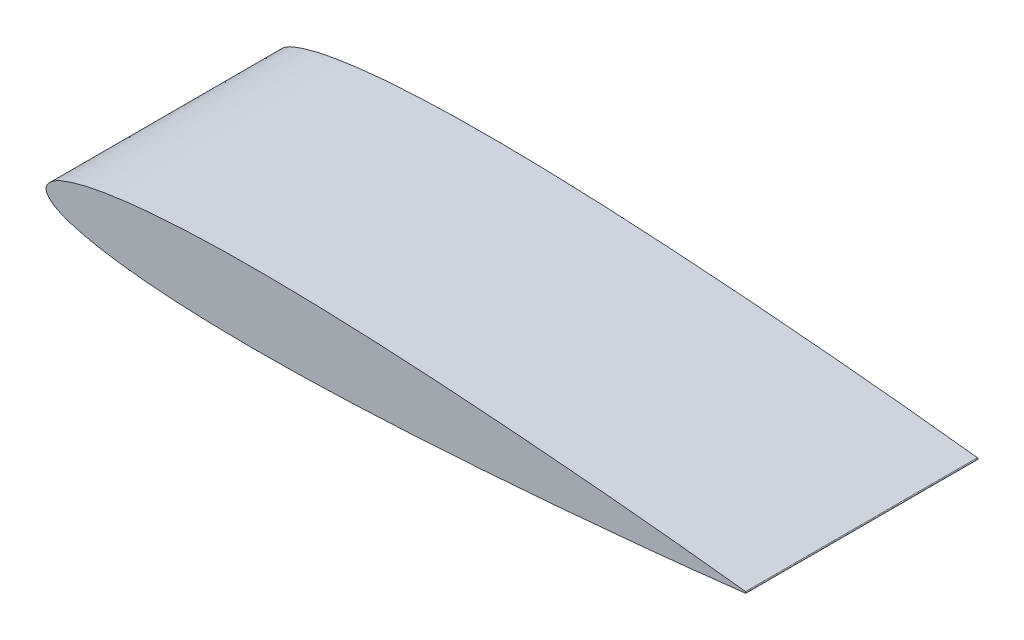
SolidWorks part; units mm, degrees
ref_plane "Front Plane" through (0, 0, 0) normal (0, 0, 1) x (1, 0, 0)
ref_plane "Top Plane" through (0, 0, 0) normal (0, 1, 0) x (1, 0, 0)
ref_plane "Right Plane" through (0, 0, 0) normal (1, 0, 0) x (0, 0, -1)
curve "Curve1"
  spline degree 3 poles (72.4, 0.076, 0) (71.1935, 0.2145, 0) (68.7814, 0.4913, 0) (63.9558, 1.0057, 0) (57.9238, 1.5969, 0) (50.6833, 2.2234, 0) (43.4435, 2.77, 0) (36.2034, 3.2155, 0) (28.9629, 3.5326, 0) (22.927, 3.6435, 0) (18.0991, 3.5996, 0) (14.4773, 3.4805, 0) (10.853, 3.2506, 0) (7.8351, 2.9304, 0) (5.42, 2.5465, 0) (3.6048, 2.1717, 0) (2.0615, 1.6954, 0) (0.7815, 1.1566, 0) (-0.4628, 0, 0) (0.7815, -1.1566, 0) (2.0615, -1.6954, 0) (3.6048, -2.1717, 0) (5.42, -2.5465, 0) (7.8351, -2.9304, 0) (10.853, -3.2506, 0) (14.4773, -3.4805, 0) (18.0991, -3.5996, 0) (22.927, -3.6435, 0) (28.9629, -3.5326, 0) (36.2034, -3.2155, 0) (43.4435, -2.77, 0) (50.6833, -2.2234, 0) (57.9238, -1.5969, 0) (63.9558, -1.0057, 0) (68.7814, -0.4913, 0) (71.1935, -0.2145, 0) (72.4, -0.076, 0) knots 0 0 0 0 0.024824 0.04963 0.099197 0.148713 0.198182 0.247604 0.29698 0.346318 0.370984 0.395664 0.420382 0.445198 0.457689 0.470304 0.483229 0.490069 0.5 0.509931 0.516771 0.529696 0.542311 0.554802 0.579618 0.604336 0.629016 0.653682 0.70302 0.752396 0.801818 0.851287 0.900803 0.95037 0.975176 1 1 1 1
sketch "Sketch1" plane through (0, 0, 0) normal (0, 0, 1) x (1, 0, 0)
  arc A0 (72.4, 0.076) -> (72.4, -0.076) centre (72.3913, 0) cw
  spline S0 degree 3 poles (708.0693, 2922.3301) (271.6381, -58.1597) (171.0391, -10.409) (63.9558, 1.0057) (57.9238, 1.5969) (50.6833, 2.2234) (43.4435, 2.77) (36.2034, 3.2155) (28.9629, 3.5326) (22.927, 3.6435) (18.0991, 3.5996) (14.4773, 3.4805) (10.853, 3.2506) (7.8351, 2.9304) (5.42, 2.5465) (3.6048, 2.1717) (2.0615, 1.6954) (0.7815, 1.1566) (-0.4628, 0) (0.7815, -1.1566) (2.0615, -1.6954) (3.6048, -2.1717) (5.42, -2.5465) (7.8351, -2.9304) (10.853, -3.2506) (14.4773, -3.4805) (18.0991, -3.5996) (22.927, -3.6435) (28.9629, -3.5326) (36.2034, -3.2155) (43.4435, -2.77) (50.6833, -2.2234) (57.9238, -1.5969) (63.9558, -1.0057) (171.0394, 10.409) (271.6388, 58.16) (708.074, -2922.3623) knots -2.102073 -2.102073 -2.102073 -2.102073 0.024824 0.04963 0.099197 0.148713 0.198182 0.247604 0.29698 0.346318 0.370984 0.395664 0.420382 0.445198 0.457689 0.470304 0.483229 0.490069 0.5 0.509931 0.516771 0.529696 0.542311 0.554802 0.579618 0.604336 0.629016 0.653682 0.70302 0.752396 0.801818 0.851287 0.900803 0.95037 0.975176 3.10208 3.10208 3.10208 3.10208 only from (72.4, 0.076) to (72.4, -0.076) construction
  spline S1 degree 3 poles (72.4, 0.076) (71.1935, 0.2145) (68.7814, 0.4913) (63.9558, 1.0057) (57.9238, 1.5969) (50.6833, 2.2234) (43.4435, 2.77) (36.2034, 3.2155) (28.9629, 3.5326) (22.927, 3.6435) (18.0991, 3.5996) (14.4773, 3.4805) (10.853, 3.2506) (7.8351, 2.9304) (5.42, 2.5465) (3.6048, 2.1717) (2.0615, 1.6954) (0.7815, 1.1566) (-0.4628, 0) (0.7815, -1.1566) (2.0615, -1.6954) (3.6048, -2.1717) (5.42, -2.5465) (7.8351, -2.9304) (10.853, -3.2506) (14.4773, -3.4805) (18.0991, -3.5996) (22.927, -3.6435) (28.9629, -3.5326) (36.2034, -3.2155) (43.4435, -2.77) (50.6833, -2.2234) (57.9238, -1.5969) (63.9558, -1.0057) (68.7814, -0.4913) (71.1935, -0.2145) (72.4, -0.076) knots 0 0 0 0 0.024824 0.04963 0.099197 0.148713 0.198182 0.247604 0.29698 0.346318 0.370984 0.395664 0.420382 0.445198 0.457689 0.470304 0.483229 0.490069 0.5 0.509931 0.516771 0.529696 0.542311 0.554802 0.579618 0.604336 0.629016 0.653682 0.70302 0.752396 0.801818 0.851287 0.900803 0.95037 0.975176 1 1 1 1
extrude "Boss-Extrude1" add sketch "Sketch1" along normal blind 24
